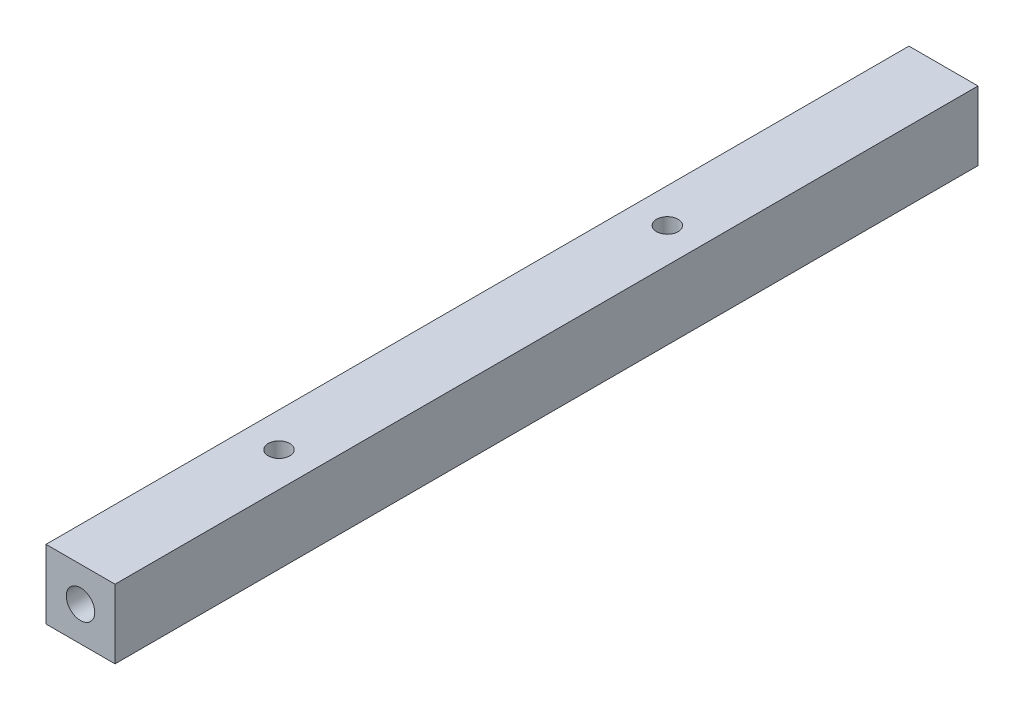
SolidWorks part; units mm, degrees
ref_plane "Front Plane" through (0, 0, 0) normal (0, 0, 1) x (1, 0, 0)
ref_plane "Top Plane" through (0, 0, 0) normal (0, 1, 0) x (1, 0, 0)
ref_plane "Right Plane" through (0, 0, 0) normal (1, 0, 0) x (0, 0, -1)
sketch "Sketch1" plane through (0, 0, 0) normal (0, 0, 1) x (1, 0, 0)
  line L1 (0, 0) -> (8, 0)
  line L2 (0, 0) -> (0, 8)
  line L3 (0, 8) -> (8, 8)
  line L4 (8, 0) -> (8, 8)
extrude "Extrude1" add sketch "Sketch1" along normal blind 100
sketch "Sketch2" plane through (0, 8, 0) normal (0, 1, 0) x (1, 0, 0)
  line L0 (4, -100) -> (4, -77) construction
  line L1 (8, -100) -> (0, -100) construction
  line L2 (4, -77) -> (4, -32) construction
  line L3 (4, -32) -> (4, 0) construction
  line L4 (8, 0) -> (0, 0) construction
hole_wizard "M3 Tapped Hole1" positions "3DSketch1" profile "Sketch3" tap size "M3" standard "DIN" end condition through all
sketch3d "3DSketch1"
  point P0 (4, 8, 77)
  point P3 (4, 8, 32)
sketch "Sketch3" plane through (4, 8, 77) normal (1, 0, 0) x (0, 0, 1)
  line L0 (0, 0) -> (0, 8)
  line L1 (0, 8) -> (1.25, 8)
  line L2 (1.25, 8) -> (1.25, 0)
  line L5 (1.25, 0) -> (0, 0)
  line L11 (0, -6.35) -> (0, 107.95) construction
  dimension "Thru Tap Drill Dia." = 2.5
  dimension "Thru Tap Drill Depth" = 8
cosmetic thread "Hole Thread1" parameters "D2"=3
cosmetic thread "Hole Thread2" parameters "D2"=3
sketch "Sketch5" plane through (0, 0, 100) normal (0, 0, 1) x (1, 0, 0)
  line L0 (0, 4) -> (8, 4) construction
  line L1 (0, 8) -> (0, 0) construction
  line L2 (8, 0) -> (8, 8) construction
  point P6 (4, 4)
sketch "Sketch6" plane through (0, 0, 0) normal (0, 0, -1) x (-1, 0, 0)
  line L0 (0, 4) -> (-8, 4) construction
  line L1 (0, 8) -> (0, 0) construction
  line L2 (-8, 0) -> (-8, 8) construction
  point P6 (-4, 4)
hole_wizard "M4 Tapped Hole1" positions "3DSketch3" profile "Sketch7" tap size "M4" standard "DIN"
sketch3d "3DSketch3"
  point P0 (4, 4, 0)
  point P3 (4, 4, 100)
sketch "Sketch7" plane through (4, 4, 0) normal (1, 0, 0) x (0, 1, 0)
  line L0 (0, 0) -> (0, 10.9914)
  line L1 (0, 10.9914) -> (1.65, 10)
  line L2 (1.65, 10) -> (1.65, 0)
  line L5 (1.65, 0) -> (0, 0)
  line L10 (0, 10.9914) -> (-1.65, 10) construction
  line L11 (0, -6.35) -> (0, 107.95) construction
  dimension "Tap Drill Dia." = 3.3
  dimension "Tap Drill Depth" = 10
  dimension "Drill Angle" = 118
cosmetic thread "Hole Thread3"
cosmetic thread "Hole Thread4"
